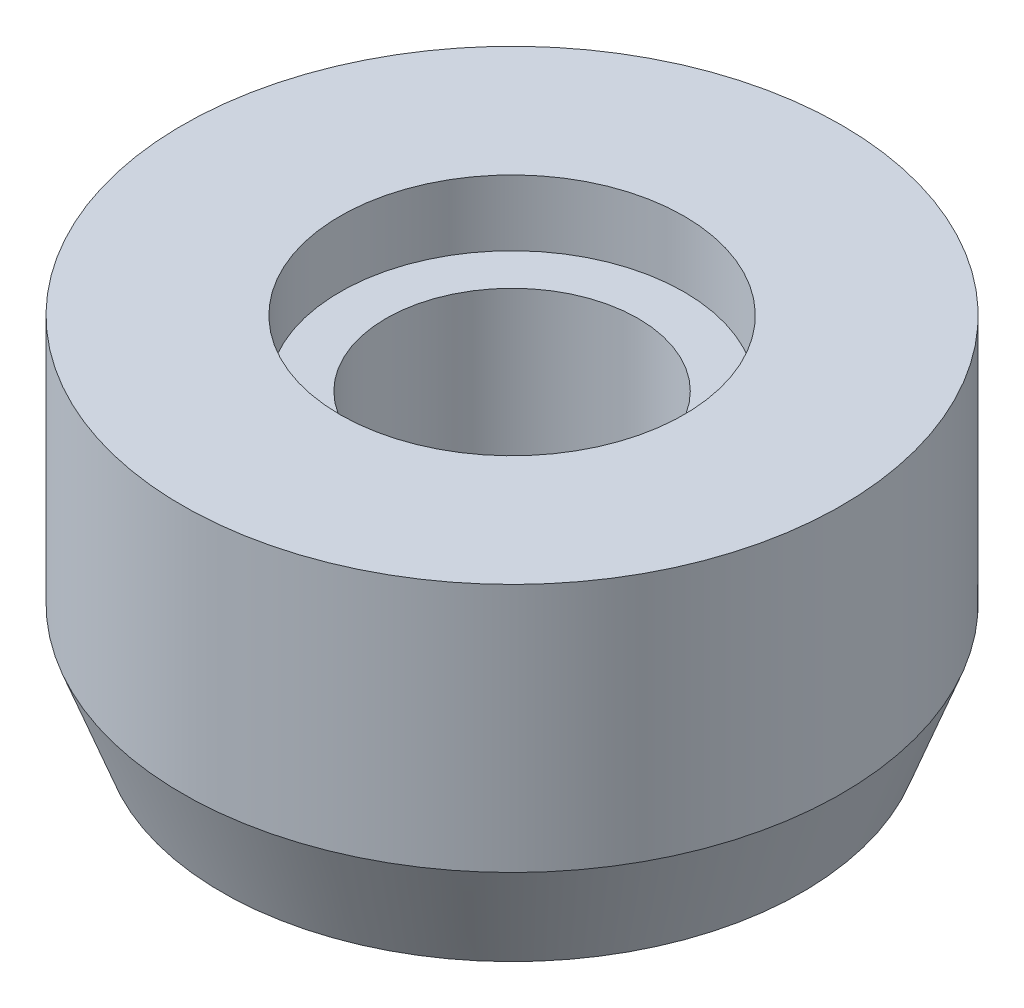
SolidWorks part; units mm, degrees
ref_plane "Front Plane" through (0, 0, 0) normal (0, 0, 1) x (1, 0, 0)
ref_plane "Top Plane" through (0, 0, 0) normal (0, 1, 0) x (1, 0, 0)
ref_plane "Right Plane" through (0, 0, 0) normal (1, 0, 0) x (0, 0, -1)
sketch "Sketch1" plane through (0, 0, 0) normal (0, 0, 1) x (1, 0, 0)
  line L0 (4.8, 0) -> (11.05, 0)
  line L1 (11.05, 0) -> (12.55, 4)
  line L2 (12.55, 4) -> (12.55, 13.5)
  line L3 (12.55, 13.5) -> (6.55, 13.5)
  line L4 (6.55, 13.5) -> (6.55, 11)
  line L5 (6.55, 11) -> (4.8, 11)
  line L6 (4.8, 11) -> (4.8, 0)
  line L7 (0, 0) -> (0, 17.1329) construction
  dimension "D1" = 9.5
  dimension "D2" = 4.8
  dimension "D3" = 4
  dimension "D4" = 1.5
  dimension "D5" = 2.5
  dimension "D6" = 6
  dimension "D7" = 1.75
revolve "Revolve1" add sketch "Sketch1" angle 360 about L7
